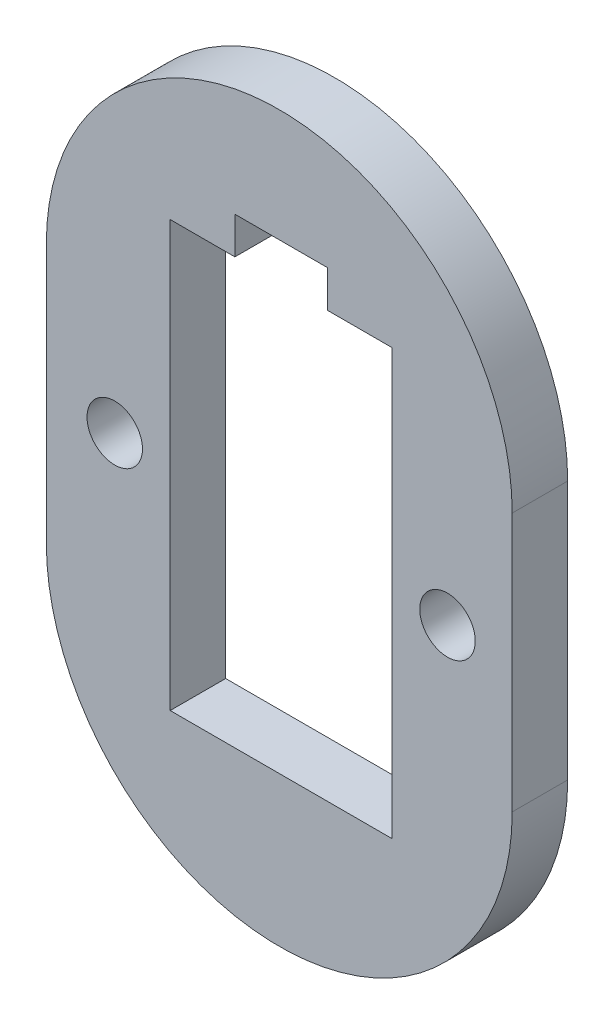
SolidWorks part; units mm, degrees
ref_plane "Front Plane" through (0, 0, 0) normal (0, 0, 1) x (1, 0, 0)
ref_plane "Top Plane" through (0, 0, 0) normal (0, 1, 0) x (1, 0, 0)
ref_plane "Right Plane" through (0, 0, 0) normal (1, 0, 0) x (0, 0, -1)
sketch "Model" plane through (0, 0, 0) normal (0, 0, 1) x (1, 0, 0)
  line L0 (19.5862, 6.709) -> (19.5862, 29.709)
  line L1 (11.0862, 29.709) -> (7.5862, 29.709)
  line L2 (11.0862, 31.709) -> (11.0862, 29.709)
  line L3 (16.0862, 31.709) -> (11.0862, 31.709)
  line L4 (16.0862, 29.709) -> (16.0862, 31.709)
  line L5 (19.5862, 29.709) -> (16.0862, 29.709)
  line L6 (0.8862, 25.2091) -> (0.8862, 11.209)
  line L7 (26.0862, 16.209) -> (26.0862, 25.209)
  line L8 (7.5862, 6.709) -> (19.5862, 6.709)
  line L9 (7.5862, 29.709) -> (7.5862, 6.709)
  line L10 (26.0862, 16.209) -> (26.0862, 11.209)
  circle A0 centre (4.5863, 18.209) radius 1.5
  circle A1 centre (22.5863, 18.209) radius 1.5
  arc A2 (26.0862, 25.209) -> (0.8862, 25.2091) centre (13.4862, 25.209) ccw
  arc A3 (0.8862, 11.209) -> (26.0862, 11.209) centre (13.4862, 11.209) ccw
extrude "Boss-Extrude1" add sketch "Model" along normal blind 3
